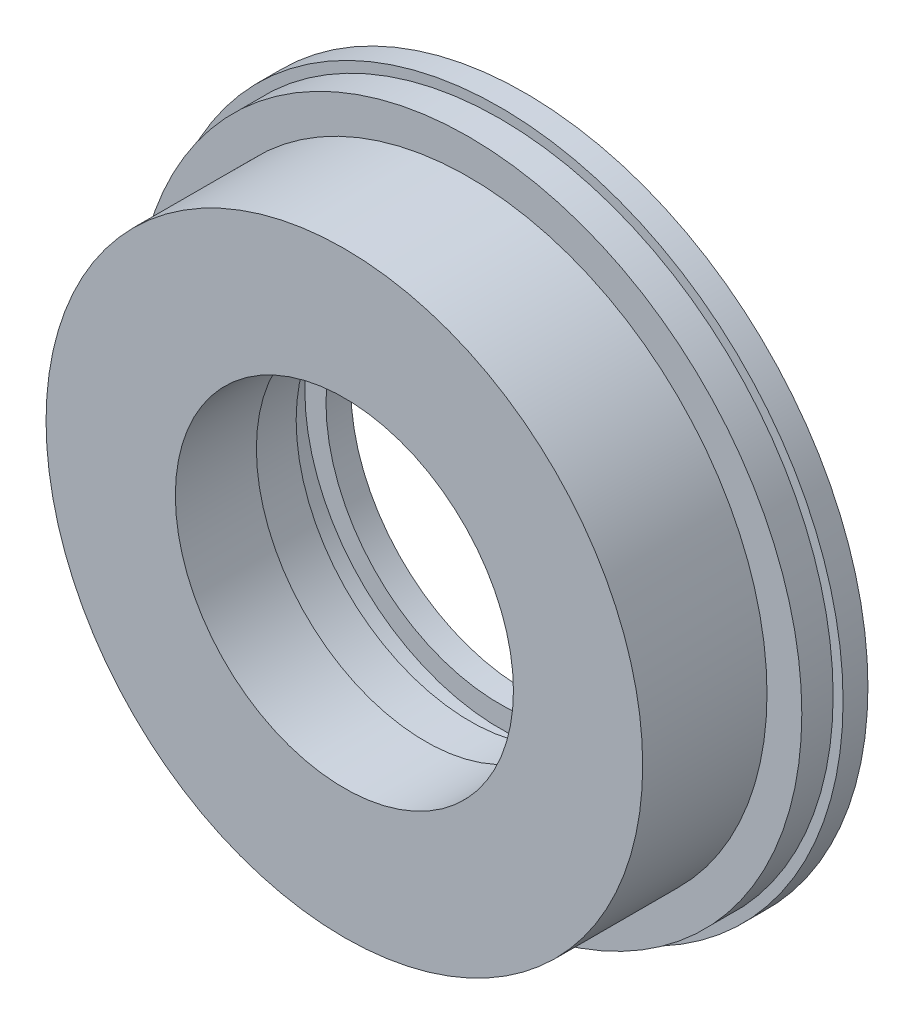
SolidWorks part; units mm, degrees
ref_plane "Front Plane" through (0, 0, 0) normal (0, 0, 1) x (1, 0, 0)
ref_plane "Top Plane" through (0, 0, 0) normal (0, 1, 0) x (1, 0, 0)
ref_plane "Right Plane" through (0, 0, 0) normal (1, 0, 0) x (0, 0, -1)
sketch "Sketch1" plane through (0, 0, 0) normal (0, 0, 1) x (1, 0, 0)
  circle A0 centre (0, 0) radius 70
  dimension "D1" = 140
extrude "Boss-Extrude1" add sketch "Sketch1" along normal mid plane 80
sketch "Sketch2" plane through (0, 0, 0) normal (0, 1, 0) x (1, 0, 0)
  line L0 (0, 0) -> (0, 61.8971) construction
  line L1 (-69, 40) -> (-69, 35)
  line L2 (-69, 35) -> (-67, 35)
  line L3 (-67, 35) -> (-67, 28.7)
  line L4 (-67, 28.7) -> (-60, 28.7)
  line L5 (-60, 28.7) -> (-60, 3.7)
  line L6 (-60, 3.7) -> (-67, 3.7)
  line L7 (-67, 3.7) -> (-67, -2.6)
  line L8 (-67, -2.6) -> (-69, -2.6)
  line L9 (-69, -2.6) -> (-69, -44.7055)
  line L10 (-69, -44.7055) -> (-73.6435, -44.7055)
  line L11 (-73.6435, -44.7055) -> (-73.6435, 40)
  line L12 (-73.6435, 40) -> (-69, 40)
  line L13 (70, 40) -> (-70, 40) construction
  dimension "D1" = 120
  dimension "D2" = 25
  dimension "D3" = 6.3
  dimension "D4" = 6.3
  dimension "D5" = 134
  dimension "D6" = 138
  dimension "D7" = 5
revolve "Cut-Revolve1" cut sketch "Sketch2" angle 360 about L0
sketch "Sketch3" plane through (0, 0, 0) normal (0, 1, 0) x (1, 0, 0)
  line L0 (0, 0) -> (0, -46.5884) construction
  line L2 (-69, -7.6) -> (-55, -7.6)
  line L3 (-69, -7.6) -> (-69, -40)
  line L4 (-69, -40) -> (-55, -40)
  line L5 (-55, -7.6) -> (-55, -40)
  line L9 (69, -2.6) -> (-69, -2.6) construction
  line L10 (-69, -40) -> (69, -40) construction
  line L11 (-69, -2.6) -> (-69, -40) construction
  dimension "D1" = 5
  dimension "D2" = 110
revolve "Cut-Revolve2" cut sketch "Sketch3" angle 360 about L0
sketch "Sketch4" plane through (0, 0, 0) normal (0, 1, 0) x (1, 0, 0)
  line L0 (0, 0) -> (0, 53.8059) construction
  line L1 (0, 42.623) -> (-35, 42.623)
  line L2 (-35, 42.623) -> (-35, 20)
  line L3 (-35, 20) -> (-34, 20)
  line L4 (-34, 20) -> (-34, -40)
  line L5 (-55, -40) -> (55, -40) construction
  line L6 (0, 42.623) -> (0, -40)
  line L7 (0, -40) -> (-34, -40)
  dimension "D1" = 60
  dimension "D2" = 68
  dimension "D3" = 70
revolve "Cut-Revolve3" cut sketch "Sketch4" angle 360 about L0
sketch "Sketch5" plane through (0, 0, 0) normal (0, 1, 0) x (1, 0, 0)
  line L0 (0, 0) -> (0, 44.7661) construction
  line L1 (-13.0161, 35) -> (-39.25, 35)
  line L2 (-13.0161, 35) -> (-13.0161, 29)
  line L3 (-13.0161, 29) -> (-39.25, 29)
  line L4 (-39.25, 35) -> (-39.25, 29)
  line L5 (35, 40) -> (-35, 40) construction
  dimension "D1" = 6
  dimension "D2" = 78.5
  dimension "D3" = 5
revolve "Cut-Revolve4" cut sketch "Sketch5" angle 360 about L0
sketch "Sketch6" plane through (0, 0, 0) normal (0, 1, 0) x (1, 0, 0)
  line L0 (67, 3.7) -> (-67, 3.7) construction
  line L1 (-75.5299, 3.7) -> (74.0633, 3.7)
  line L2 (-75.5299, 3.7) -> (-75.5299, -46.3477)
  line L3 (-75.5299, -46.3477) -> (74.0633, -46.3477)
  line L4 (74.0633, 3.7) -> (74.0633, -46.3477)
extrude "Cut-Extrude1" cut sketch "Sketch6" against normal mid plane 172
